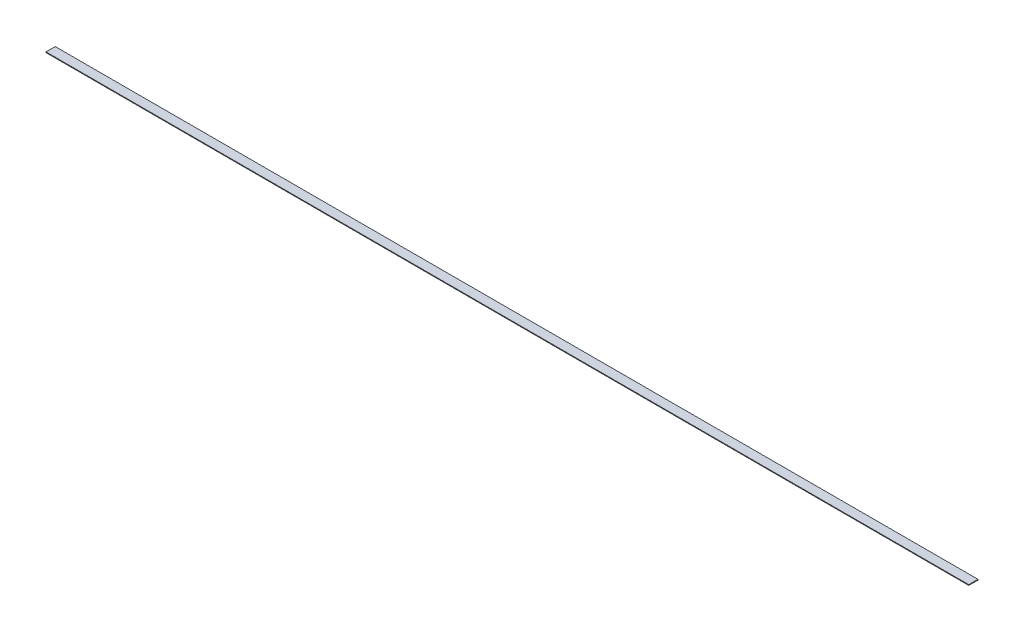
SolidWorks part; units mm, degrees
ref_plane "Спереди" through (0, 0, 0) normal (0, 0, 1) x (1, 0, 0)
ref_plane "Сверху" through (0, 0, 0) normal (0, 1, 0) x (1, 0, 0)
ref_plane "Справа" through (0, 0, 0) normal (1, 0, 0) x (0, 0, -1)
sketch "Эскиз1" plane through (0, 0, 0) normal (1, 0, 0) x (0, 0, -1)
  line L1 (-10, -0.75) -> (10, -0.75)
  line L2 (-10, -0.75) -> (-10, 0.75)
  line L3 (-10, 0.75) -> (10, 0.75)
  line L4 (10, -0.75) -> (10, 0.75)
  line L5 (-10, -0.75) -> (10, 0.75) construction
  line L6 (-10, 0.75) -> (10, -0.75) construction
  point P0 (0, 0)
  dimension "D1" = 1.5
  dimension "D2" = 20
extrude "Бобышка-Вытянуть1" add sketch "Эскиз1" along normal blind 2000
